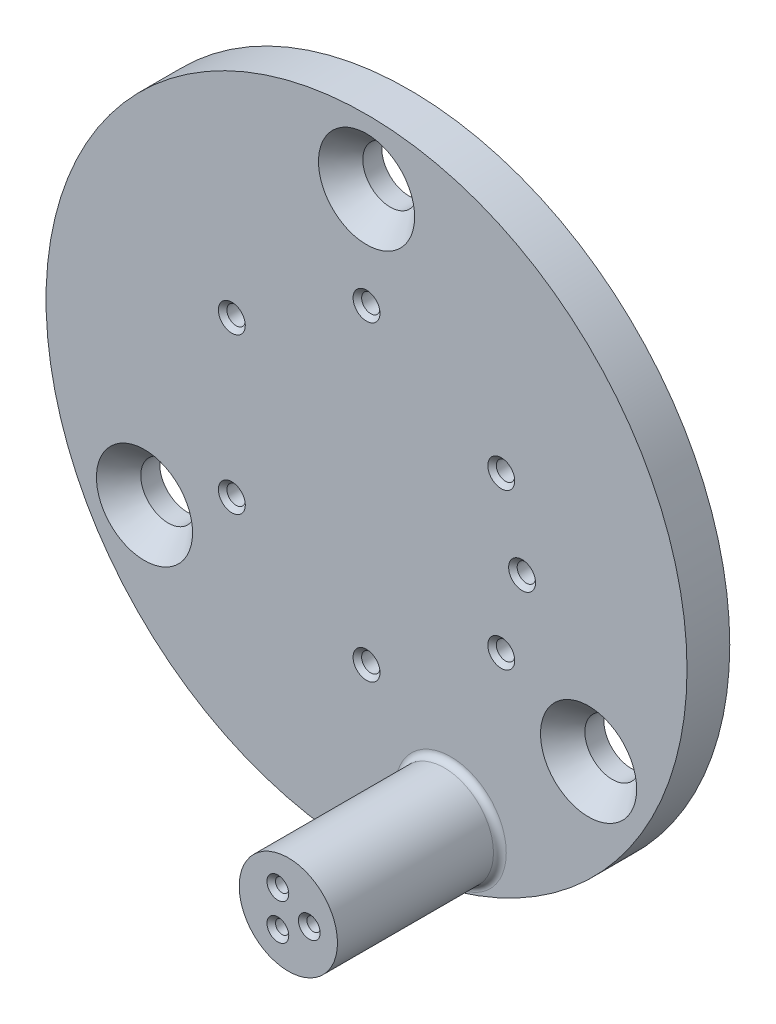
SolidWorks part; units mm, degrees
material "PEEK"
ref_plane "Front" through (0, 0, 0) normal (0, 0, 1) x (1, 0, 0)
ref_plane "Top" through (0, 0, 0) normal (0, 1, 0) x (1, 0, 0)
ref_plane "Right" through (0, 0, 0) normal (1, 0, 0) x (0, 0, -1)
sketch "Sketch1" plane through (0, 0, 0) normal (0, 0, 1) x (1, 0, 0)
  circle A0 centre (-17.7662, -20.0165) radius 19.05
  dimension "D1" = 38.1
extrude "Boss-Extrude1" add sketch "Sketch1" along normal blind 2.54
hole_wizard "CSK for #4 Flat Head Machine Screw1" positions "Sketch3" profile "Sketch2" countersink size "#4" standard "Ansi Inch" end condition through all
sketch "Sketch3" plane through (-8.523, 17.8442, 2.54) normal (0, 0, 1) x (1, 0, 0)
  point P21 (-22.4415, -45.5221)
  point P24 (-9.2432, -22.6621)
  point P27 (3.955, -45.5221)
sketch "Sketch2" plane through (-30.9645, -27.6779, 2.54) normal (1, 0, 0) x (0, -1, 0)
  line L0 (0, 0) -> (0, 2.54)
  line L1 (0, 2.54) -> (1.6319, 2.54)
  line L2 (1.6319, 2.54) -> (1.6319, 1.4098)
  line L3 (1.6319, 1.4098) -> (2.8575, 0)
  line L5 (2.8575, 0) -> (0, 0)
  line L6 (-1.632, 1.4098) -> (-2.8575, 0) construction
  line L11 (0, -6.35) -> (0, 107.95) construction
  dimension "Thru Hole Dia." = 3.2639
  dimension "Thru Hole Depth" = 2.54
  dimension "Near C'Sink Dia." = 5.715
  dimension "Near C'Sink Angle" = 82
hole_wizard "#57 (0.043) Diameter Hole1" positions "Sketch5" profile "Sketch4" hole size "#57" standard "Ansi Inch" end condition through all
sketch "Sketch5" plane through (0, 0, 2.54) normal (0, 0, 1) x (1, 0, 0)
  point P2 (-17.7662, -10.8123)
  point P5 (-25.7732, -15.4351)
  point P8 (-9.7593, -15.4351)
  point P11 (-8.5206, -20.0579)
  point P14 (-9.7593, -24.6807)
  point P17 (-17.7662, -29.3035)
  point P20 (-25.7732, -24.6807)
sketch "Sketch4" plane through (-17.7662, -10.8123, 2.54) normal (1, 0, 0) x (0, -1, 0)
  line L0 (0, 0) -> (0, 2.54)
  line L1 (0, 2.54) -> (0.5461, 2.54)
  line L2 (0.5461, 2.54) -> (0.5461, 0)
  line L5 (0.5461, 0) -> (0, 0)
  line L11 (0, -6.35) -> (0, 107.95) construction
  dimension "Thru Hole Dia." = 1.0922
  dimension "Thru Hole Depth" = 2.54
sketch "Sketch9" plane through (0, 0, 2.54) normal (0, 0, 1) x (1, 0, 0)
  line L0 (-12.7624, -36.0745) -> (-12.7624, -33.5853) construction
  circle A0 centre (-12.7624, -34.8299) radius 2.921
  circle A1 centre (-12.7624, -36.0745) radius 0.3175 construction
  circle A2 centre (-12.7624, -33.5853) radius 0.3175 construction
  dimension "D1" = 5.842
extrude "Boss-Extrude2" add sketch "Sketch9" along normal blind 9.652
chamfer "Chamfer1" distance 0.254 angle 45 7 edges at (-9.2132, -15.4351, 2.54) (-7.9745, -20.0579, 2.54) (-9.2132, -24.6807, 2.54) (-17.2201, -29.3035, 2.54) (-25.2271, -24.6807, 2.54) (-25.2271, -15.4351, 2.54) (-17.2201, -10.8123, 2.54)
hole_wizard "#68 (0.031) Diameter Hole2" positions "Sketch11" profile "Sketch10" hole size "#68" standard "Ansi Inch" end condition through all
sketch "Sketch11" plane through (0, 0, 12.192) normal (0, 0, 1) x (1, 0, 0)
  line L0 (-12.7624, -33.5853) -> (-12.7624, -36.0745) construction
  line L2 (-12.7624, -34.8299) -> (-11.5178, -34.8299) construction
  line L4 (-12.7624, -34.8299) -> (-13.3847, -33.7521) construction
  line L6 (-12.7624, -34.8299) -> (-13.3847, -35.9078) construction
  circle A0 centre (-12.7624, -34.8299) radius 1.2446 construction
  point P0 (-13.3847, -33.7521)
  point P1 (-13.3847, -35.9078)
  point P3 (-11.5178, -34.8299)
  dimension "D3" = 2.4892
  dimension "D1" = 120
  dimension "D2" = 120
sketch "Sketch10" plane through (-13.3847, -33.7521, 12.192) normal (1, 0, 0) x (0, -1, 0)
  line L0 (0, 0) -> (0, 12.192)
  line L1 (0, 12.192) -> (0.3937, 12.192)
  line L2 (0.3937, 12.192) -> (0.3937, 0)
  line L5 (0.3937, 0) -> (0, 0)
  line L11 (0, -6.35) -> (0, 107.95) construction
  dimension "Thru Hole Dia." = 0.7874
  dimension "Thru Hole Depth" = 12.192
chamfer "Chamfer2" distance 0.254 angle 45 3 edges at (-11.1241, -34.8299, 12.192) (-12.991, -35.9078, 12.192) (-12.991, -33.7521, 12.192)
chamfer "Chamfer3" distance 0.254 angle 45 10 edges at (-9.2132, -24.6807, 0) (-17.2201, -29.3035, 0) (-25.2271, -24.6807, 0) (-25.2271, -15.4351, 0) (-7.9745, -20.0579, 0) (-9.2132, -15.4351, 0) (-17.2201, -10.8123, 0) (-12.991, -35.9078, 0) (-11.1241, -34.8299, 0) (-12.991, -33.7521, 0)
fillet "Fillet1" radius 0.381 1 edges at (-9.8414, -34.8299, 2.54)
